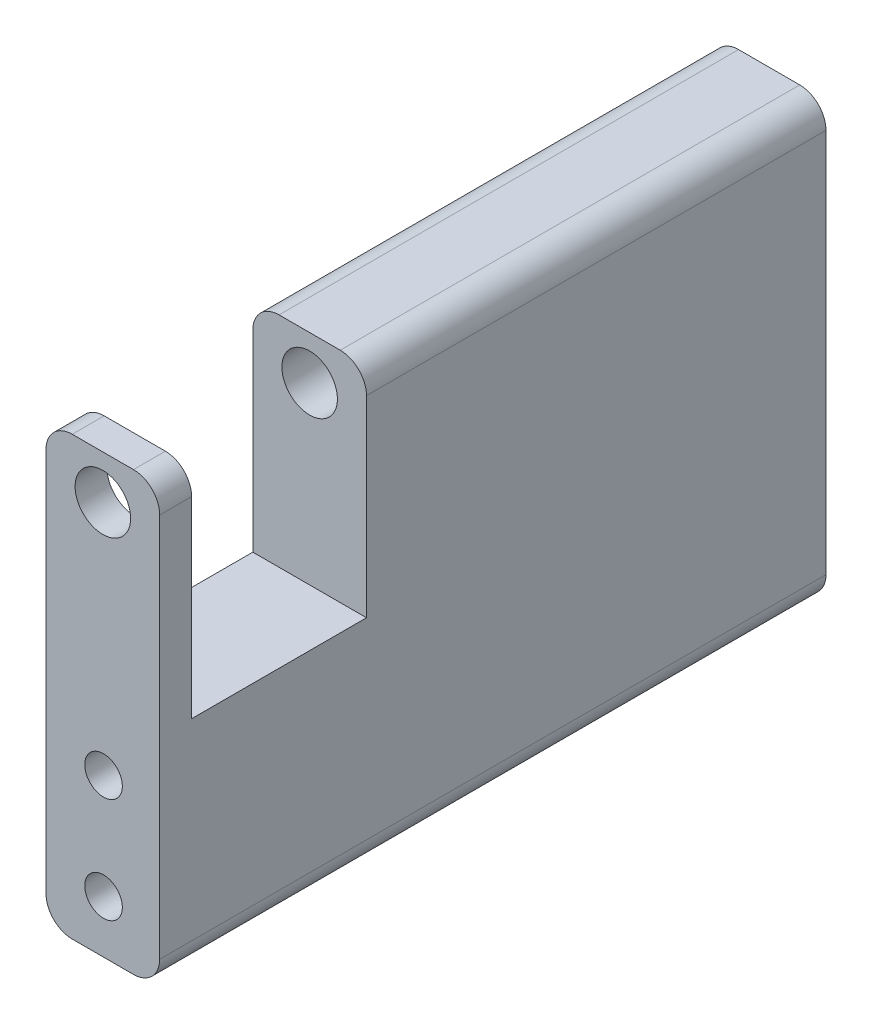
SolidWorks part; units mm, degrees
ref_plane "Front Plane" through (0, 0, 0) normal (0, 0, 1) x (1, 0, 0)
ref_plane "Top Plane" through (0, 0, 0) normal (0, 1, 0) x (1, 0, 0)
ref_plane "Right Plane" through (0, 0, 0) normal (1, 0, 0) x (0, 0, -1)
sketch "Sketch1" plane through (0, 0, 0) normal (0, 0, 1) x (1, 0, 0)
  line L0 (6.5, 0) -> (6.5, 50) construction
  line L5 (0, 0) -> (13, 0)
  line L6 (0, 0) -> (0, 50)
  line L7 (0, 50) -> (13, 50)
  line L8 (13, 0) -> (13, 50)
  circle A0 centre (6.5, 45) radius 3.175
  dimension "D2" = 6.35
  dimension "D1" = 5
  dimension "D3" = 13
  dimension "D4" = 50
extrude "Boss-Extrude1" add sketch "Sketch1" along normal blind 76.2
ref_plane "Plane1" through (0, 0, 62.55) normal (0, 0, 1) x (1, 0, 0)
sketch "Sketch2" plane through (0, 0, 62.55) normal (0, 0, 1) x (1, 0, 0)
  line L0 (0, 50) -> (0, 0) construction
  line L2 (0, 50) -> (13, 50)
  line L4 (0, 50) -> (0, 25)
  line L5 (0, 25) -> (13, 25)
  line L6 (13, 0) -> (13, 50) construction
  line L7 (13, 25) -> (13, 50)
  dimension "D1" = 25
extrude "Cut-Extrude1" cut sketch "Sketch2" against normal mid plane 20
hole_wizard "M4 Clearance Hole1" positions "Sketch3" profile "Sketch6" hole size "M4" standard "ANSI Metric"
sketch "Sketch3" plane through (0, 0, 0) normal (0, 0, -1) x (-1, 0, 0)
  line L0 (0, 0) -> (-13, 0) construction
  point P0 (-6.5792, 18)
  point P2 (-6.5792, 6)
  dimension "D1" = 6
  dimension "D2" = 12
sketch "Sketch6" plane through (6.5792, 18, 0) normal (1, 0, 0) x (0, 1, 0)
  line L0 (0, 0) -> (0, 6.2919)
  line L1 (0, 6.2919) -> (2.15, 5)
  line L2 (2.15, 5) -> (2.15, 0)
  line L5 (2.15, 0) -> (0, 0)
  line L10 (0, 6.2919) -> (-2.15, 5) construction
  line L11 (0, -6.35) -> (0, 107.95) construction
  dimension "Hole Dia." = 4.3
  dimension "Hole Depth" = 5
  dimension "Drill Angle" = 118
hole_wizard "M4 Clearance Hole2" positions "Sketch7" profile "Sketch8" hole size "M4" standard "ANSI Metric"
sketch "Sketch7" plane through (0, 0, 76.2) normal (0, 0, 1) x (1, 0, 0)
  point P0 (6.5792, 18)
  point P3 (6.5792, 6)
sketch "Sketch8" plane through (6.5792, 18, 76.2) normal (1, 0, 0) x (0, -1, 0)
  line L0 (0, 0) -> (0, 6.2919)
  line L1 (0, 6.2919) -> (2.15, 5)
  line L2 (2.15, 5) -> (2.15, 0)
  line L5 (2.15, 0) -> (0, 0)
  line L10 (0, 6.2919) -> (-2.15, 5) construction
  line L11 (0, -6.35) -> (0, 107.95) construction
  dimension "Hole Dia." = 4.3
  dimension "Hole Depth" = 5
  dimension "Drill Angle" = 118
fillet "Fillet1" radius 3 6 edges at (0, 0, 38.1) (13, 0, 38.1) (0, 50, 74.375) (13, 50, 74.375) (0, 50, 26.275) (13, 50, 26.275)
